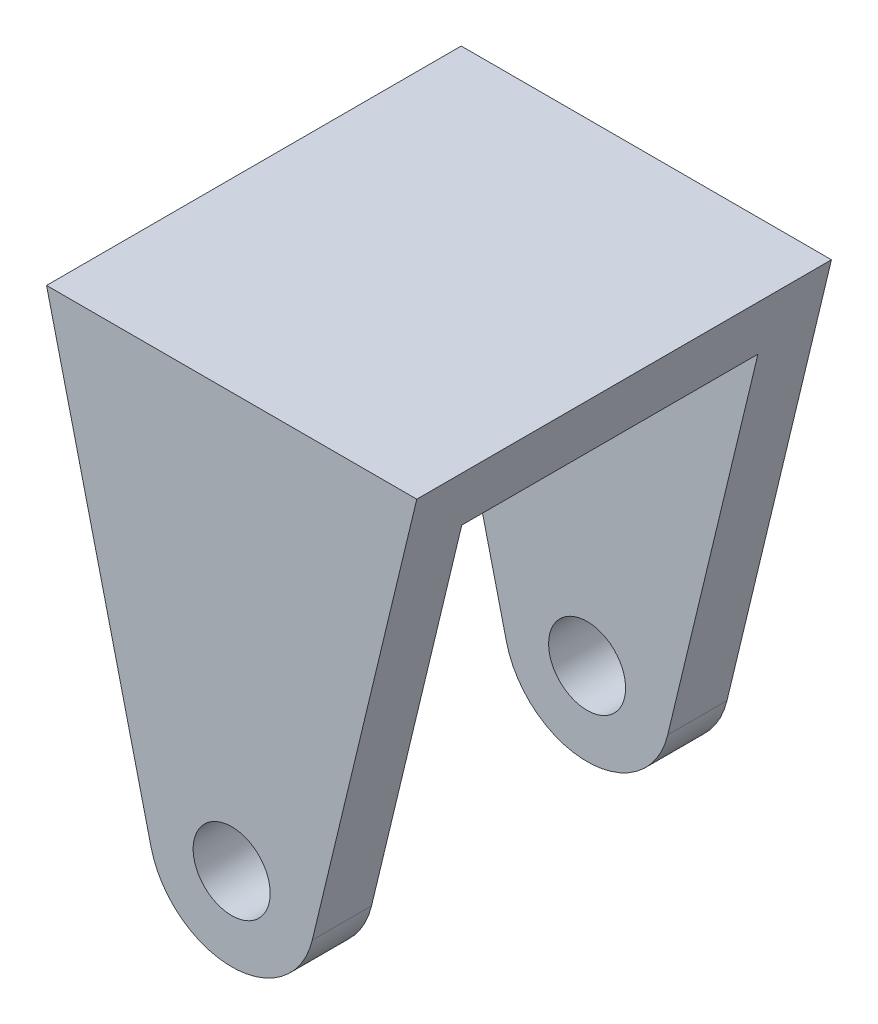
SolidWorks part; units mm, degrees
ref_plane "Front Plane" through (0, 0, 0) normal (0, 0, 1) x (1, 0, 0)
ref_plane "Top Plane" through (0, 0, 0) normal (0, 1, 0) x (1, 0, 0)
ref_plane "Right Plane" through (0, 0, 0) normal (1, 0, 0) x (0, 0, -1)
sketch "Sketch1" plane through (0, 0, 0) normal (0, 0, 1) x (1, 0, 0)
  line L0 (-125, 280) -> (125, 280)
  line L1 (125, 280) -> (54.4448, -13.1057)
  line L3 (-125, 280) -> (-54.4448, -13.1057)
  circle A0 centre (0, 0) radius 26
  circle A1 centre (0, 0) radius 56
  point P9 (52.8834, -18.3325)
  point P10 (0, 280)
  point P11 (-107.9606, 251.4847)
  dimension "D1" = 52
  dimension "D2" = 30
  dimension "D3" = 280
  dimension "D4" = 250
extrude "Boss-Extrude1" add sketch "Sketch1" along normal mid plane 280 contours A1 L1 L0 L3 | A1 A0
sketch "Sketch2" plane through (0, 0, 0) normal (1, 0, 0) x (0, 0, -1)
  line L0 (-140, -56) -> (140, -56) construction
  line L1 (-100, -56) -> (100, -56)
  line L2 (-100, -56) -> (-100, 240)
  line L3 (-100, 240) -> (100, 240)
  line L4 (100, -56) -> (100, 240)
  line L5 (-140, 280) -> (140, 280) construction
  point P6 (0, 240)
  dimension "D1" = 40
  dimension "D2" = 200
extrude "Cut-Extrude1" cut sketch "Sketch2" against normal through all both and the other way through all
